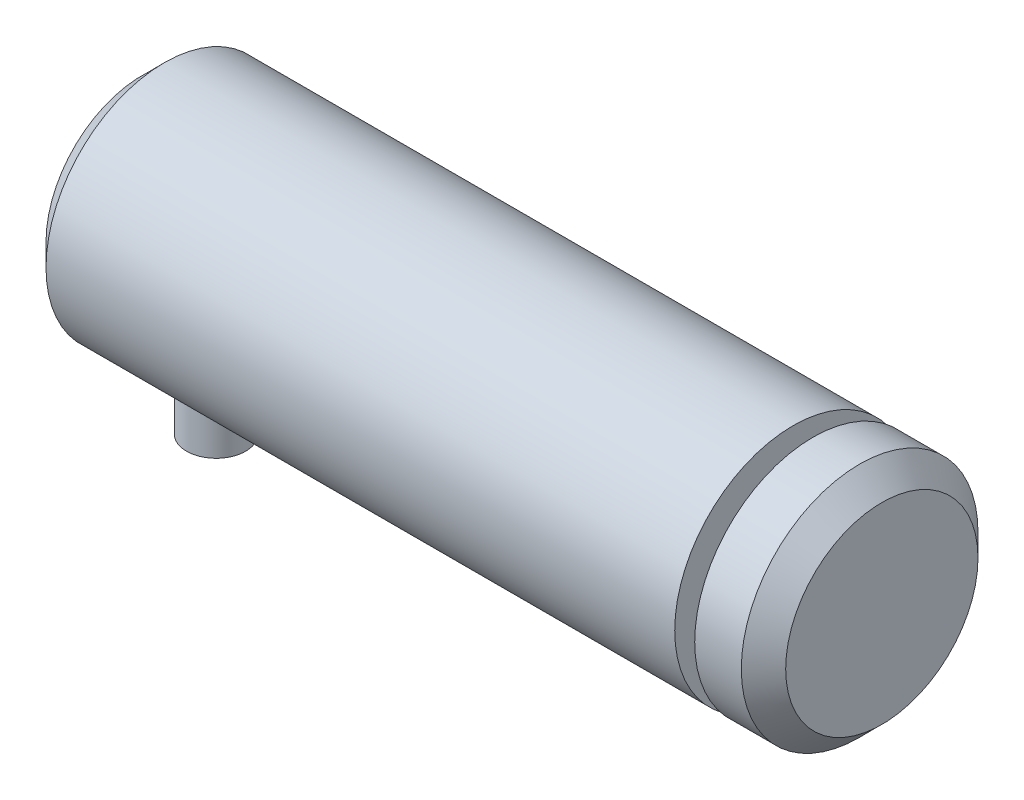
SolidWorks part; units mm, degrees
ref_plane "Front Plane" through (0, 0, 0) normal (0, 0, 1) x (1, 0, 0)
ref_plane "Top Plane" through (0, 0, 0) normal (0, 1, 0) x (1, 0, 0)
ref_plane "Right Plane" through (0, 0, 0) normal (1, 0, 0) x (0, 0, -1)
ref_plane "Plane1" through (0, 0, 0) normal (0, 0, 1) x (1, 0, 0)
sketch "Sketch1" plane through (0, 0, 0) normal (0, 0, 1) x (1, 0, 0)
  line L0 (-25, 0) -> (-25, 8)
  line L1 (-25, 8) -> (19, 8)
  line L2 (19, 8) -> (19, 0)
  line L3 (19, 0) -> (-25, 0)
  line L4 (19, 0) -> (-25, 0) construction
revolve "Revolve1" add sketch "Sketch1" angle 360 about L4
ref_plane "Plane2" through (0, 0, 0) normal (0, 0, 1) x (1, 0, 0)
sketch "Sketch2" plane through (0, 0, 0) normal (0, 0, 1) x (1, 0, 0)
  line L0 (-25, 6.5) -> (-23.5, 8)
  line L1 (-23.5, 8) -> (-25, 8)
  line L2 (-25, 8) -> (-25, 6.5)
  line L3 (39, 0) -> (-39, 0) construction
revolve "Cut-Revolve1" cut sketch "Sketch2" angle 360 about L3
ref_plane "Plane3" through (0, 0, 0) normal (0, 1, 0) x (1, 0, 0)
sketch "Sketch3" plane through (0, 0, 0) normal (0, 1, 0) x (1, 0, 0)
  circle A0 centre (-20, 0) radius 2
extrude "Boss-Extrude1" add sketch "Sketch3" against normal blind 12
ref_plane "Plane4" through (0, 0, 0) normal (0, 0, 1) x (1, 0, 0)
sketch "Sketch4" plane through (0, 0, 0) normal (0, 0, 1) x (1, 0, 0)
  line L0 (19, 0) -> (19, 8)
  line L1 (19, 8) -> (25, 8)
  line L2 (25, 8) -> (25, 0)
  line L3 (25, 0) -> (19, 0)
  line L4 (25, 0) -> (19, 0) construction
revolve "Revolve2" add sketch "Sketch4" angle 360 about L4
ref_plane "Plane5" through (0, 0, 0) normal (0, 0, 1) x (1, 0, 0)
sketch "Sketch5" plane through (0, 0, 0) normal (0, 0, 1) x (1, 0, 0)
  line L0 (19, 6) -> (20.35, 6)
  line L1 (20.35, 6) -> (20.35, 8)
  line L2 (20.35, 8) -> (19, 8)
  line L3 (19, 8) -> (19, 6)
  line L4 (39, 0) -> (-39, 0) construction
revolve "Cut-Revolve2" cut sketch "Sketch5" angle 360 about L4
ref_plane "Plane6" through (0, 0, 0) normal (0, 0, 1) x (1, 0, 0)
sketch "Sketch6" plane through (0, 0, 0) normal (0, 0, 1) x (1, 0, 0)
  line L0 (23.5, 8) -> (25, 6.5)
  line L1 (25, 6.5) -> (25, 8)
  line L2 (25, 8) -> (23.5, 8)
  line L3 (39, 0) -> (-39, 0) construction
revolve "Cut-Revolve3" cut sketch "Sketch6" angle 360 about L3
